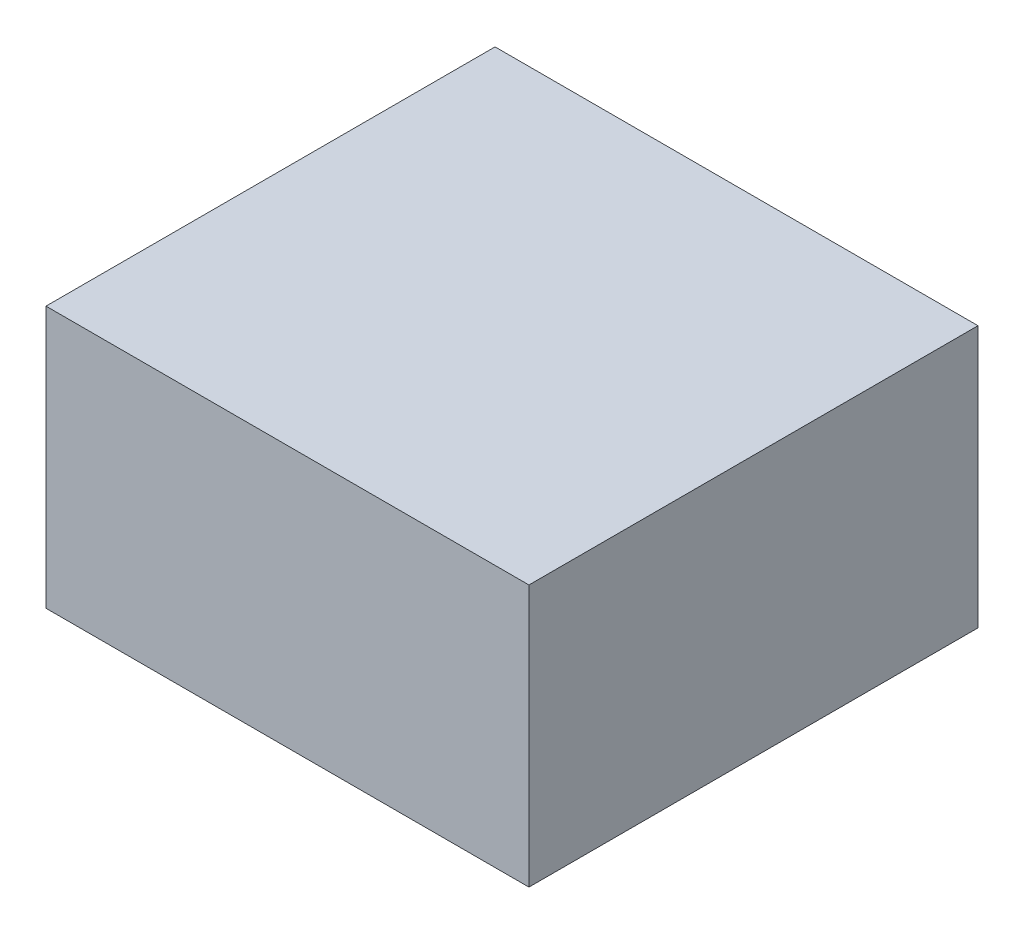
SolidWorks part; units mm, degrees
ref_plane "Front" through (0, 0, 0) normal (0, 0, 1) x (1, 0, 0)
ref_plane "Top" through (0, 0, 0) normal (0, 1, 0) x (1, 0, 0)
ref_plane "Right" through (0, 0, 0) normal (1, 0, 0) x (0, 0, -1)
sketch "Sketch1" plane through (0, 0, 0) normal (0, 1, 0) x (1, 0, 0)
  line L1 (0, 0) -> (103.124, 0)
  line L2 (0, 0) -> (0, -95.885)
  line L3 (0, -95.885) -> (103.124, -95.885)
  line L4 (103.124, 0) -> (103.124, -95.885)
  dimension "D1" = 103.124
  dimension "D2" = 95.885
extrude "Extrude1" add sketch "Sketch1" along normal blind 55.88
